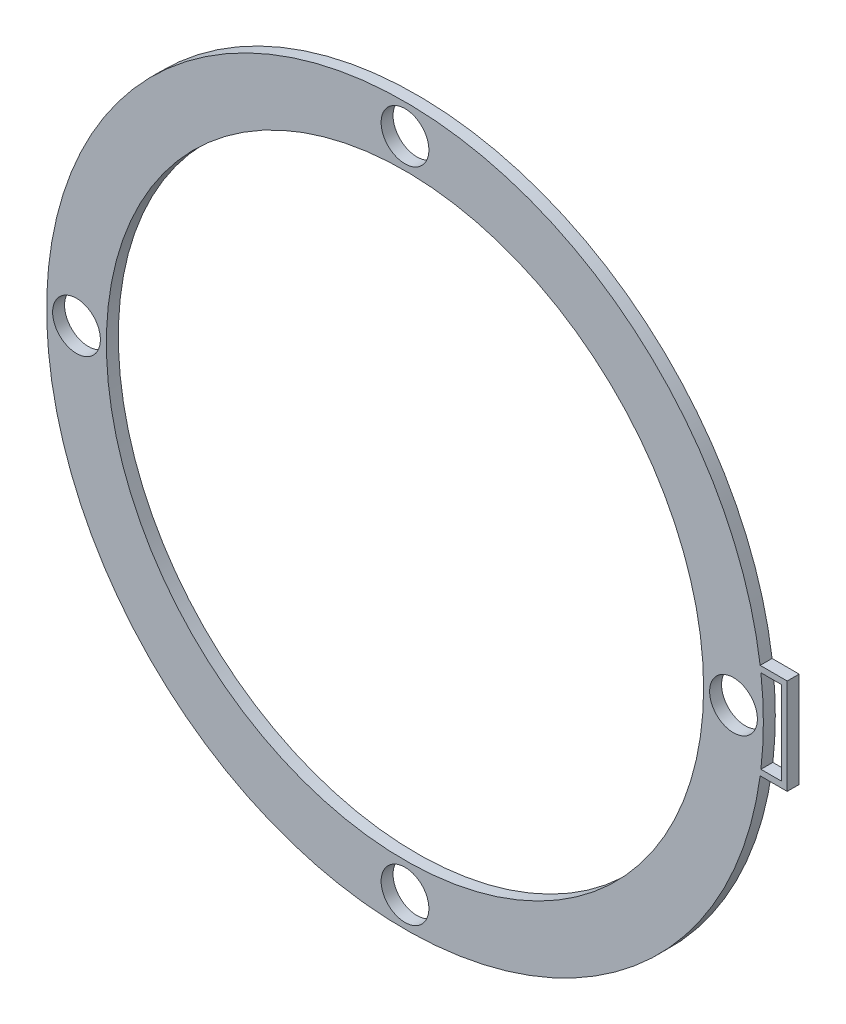
SolidWorks part; units mm, degrees
ref_plane "Alzado" through (0, 0, 0) normal (0, 0, 1) x (1, 0, 0)
ref_plane "Planta" through (0, 0, 0) normal (0, 1, 0) x (1, 0, 0)
ref_plane "Vista lateral" through (0, 0, 0) normal (1, 0, 0) x (0, 0, -1)
sketch "Croquis1" plane through (0, 0, 0) normal (0, 0, 1) x (1, 0, 0)
  line L0 (60, 0) -> (60, -7) construction
  line L1 (60, 0) -> (70, 0) construction
  line L2 (60, -7) -> (59.5903, -7)
  line L3 (60, -7) -> (63, -7)
  line L4 (63, -7) -> (63, 7)
  line L5 (60, 7) -> (59.5903, 7)
  line L6 (63.9953, 8.0061) -> (63.9953, -8.0061)
  line L7 (63.9953, -8.0061) -> (59.4634, -8.0061)
  line L8 (63.9953, 8.0061) -> (59.4634, 8.0061)
  line L9 (60, 7) -> (63, 7)
  line L10 (60, 0) -> (50, 0) construction
  circle A0 centre (0, 0) radius 50
  circle A1 centre (0, 0) radius 60
  circle A2 centre (55, 0) radius 4
  circle A3 centre (0, -55) radius 4
  circle A4 centre (-55, 0) radius 4
  circle A5 centre (0, 55) radius 4
  point P16 (63, 0)
  point P17 (63.9953, 0)
  point P30 (0, 0)
  dimension "D1" = 4
extrude "Saliente-Extruir1" add sketch "Croquis1" along normal blind 2 contours A1 A5 A4 A3 A2 A0 | A1 L5 L9 L4 L3 L2 L7 L6 L8
scale "Escala1" scale about centroid uniform scaling yes scale factor 0.5
